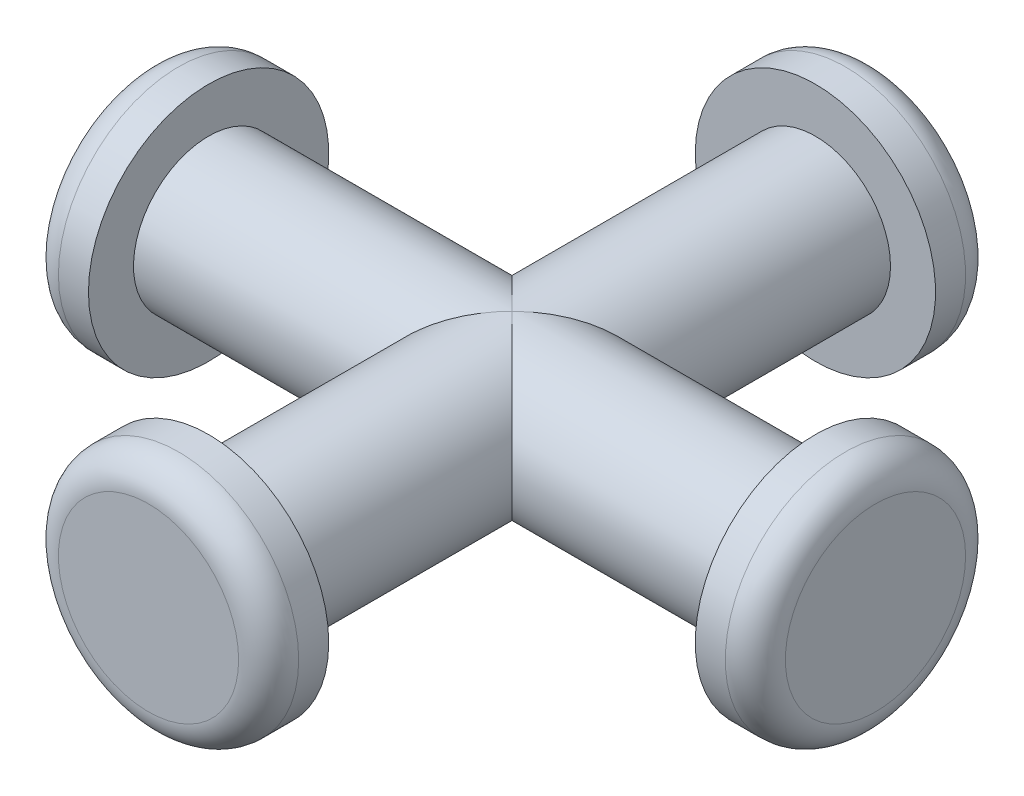
SolidWorks part; units mm, degrees
ref_plane "Plan de face" through (0, 0, 0) normal (0, 0, 1) x (1, 0, 0)
ref_plane "Plan de dessus" through (0, 0, 0) normal (0, 1, 0) x (1, 0, 0)
ref_plane "Plan de droite" through (0, 0, 0) normal (1, 0, 0) x (0, 0, -1)
sketch "Esquisse1" plane through (0, 0, 0) normal (0, 0, 1) x (1, 0, 0)
  circle A0 centre (0, 0) radius 2.5
  dimension "D1" = 5
extrude "Boss.-Extru.1" add sketch "Esquisse1" along normal mid plane 20.2 contours A0
sketch "Esquisse3" plane through (0, 0, 0) normal (1, 0, 0) x (0, 0, -1)
  circle A0 centre (0, 0) radius 2.5
  dimension "D1" = 5
extrude "Boss.-Extru.2" add sketch "Esquisse3" along normal mid plane 20.2
sketch "Esquisse4" plane through (10.1, 0, 0) normal (1, 0, 0) x (0, 0, -1)
  circle A0 centre (0, 0) radius 4
  dimension "D1" = 8
extrude "Boss.-Extru.3" add sketch "Esquisse4" along normal blind 2 contours A0
sketch "Esquisse5" plane through (-10.1, 0, 0) normal (-1, 0, 0) x (0, 0, 1)
  circle A0 centre (0, 0) radius 4
  dimension "D1" = 8
extrude "Boss.-Extru.4" add sketch "Esquisse5" along normal blind 2
sketch "Esquisse6" plane through (0, 0, 10.1) normal (0, 0, 1) x (1, 0, 0)
  circle A0 centre (0, 0) radius 4
  dimension "D1" = 8
extrude "Boss.-Extru.5" add sketch "Esquisse6" along normal blind 2
sketch "Esquisse7" plane through (0, 0, -10.1) normal (0, 0, -1) x (-1, 0, 0)
  circle A0 centre (0, 0) radius 4
  dimension "D1" = 8
extrude "Boss.-Extru.6" add sketch "Esquisse7" along normal blind 2 contours A0
fillet "Congé1" radius 1 4 edges at (-12.1, 0, 4) (-4, 0, -12.1) (12.1, 0, -4) (4, 0, 12.1)
